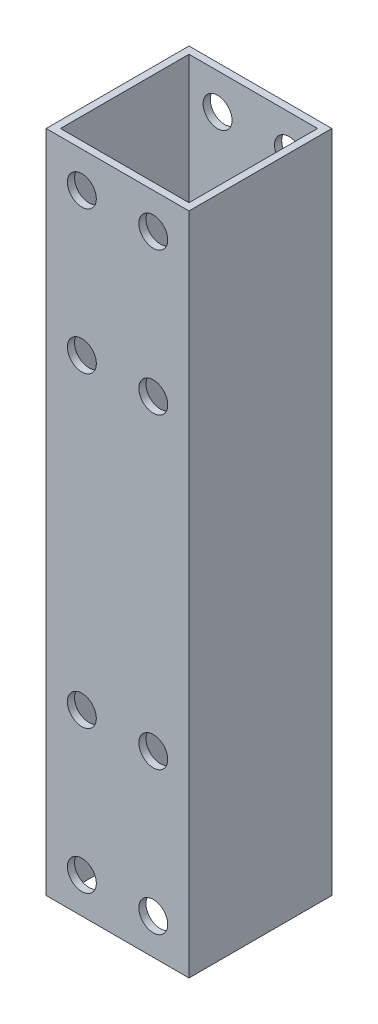
SolidWorks part; units mm, degrees
material "6061 合金"
ref_plane "前视基准面" through (0, 0, 0) normal (0, 0, 1) x (1, 0, 0)
ref_plane "上视基准面" through (0, 0, 0) normal (0, 1, 0) x (1, 0, 0)
ref_plane "右视基准面" through (0, 0, 0) normal (1, 0, 0) x (0, 0, -1)
sketch "草图1" plane through (0, 0, 0) normal (0, 1, 0) x (1, 0, 0)
  line L0 (-9, 9) -> (9, 9)
  line L1 (-10, 10) -> (10, 10)
  line L2 (-10, 10) -> (-10, -10)
  line L3 (-10, -10) -> (10, -10)
  line L4 (10, 10) -> (10, -10)
  line L5 (0, -10) -> (0, 10) construction
  line L6 (-10, 0) -> (10, 0) construction
  line L7 (9, 9) -> (9, -9)
  line L8 (-9, -9) -> (9, -9)
  line L9 (-9, 9) -> (-9, -9)
  point P0 (0, 0)
  dimension "D1" = 20
  dimension "D2" = 20
  dimension "D3" = 1
extrude "凸台-拉伸1" add sketch "草图1" along normal blind 93
sketch "草图2" plane through (0, 0, 10) normal (0, 0, 1) x (1, 0, 0)
  line L0 (-10, 0) -> (10, 0) construction
  line L1 (-5, 25) -> (5, 25) construction
  line L2 (-5, 25) -> (-5, 5) construction
  line L3 (-5, 5) -> (5, 5) construction
  line L4 (5, 25) -> (5, 5) construction
  line L5 (0, 5) -> (0, 25) construction
  line L6 (-5, 15) -> (5, 15) construction
  line L7 (-10, 93) -> (10, 93) construction
  line L8 (-5, 88) -> (5, 88) construction
  line L9 (-5, 88) -> (-5, 68) construction
  line L10 (-5, 68) -> (5, 68) construction
  line L11 (5, 88) -> (5, 68) construction
  line L12 (0, 68) -> (0, 88) construction
  line L13 (-5, 78) -> (5, 78) construction
  circle A0 centre (-5, 5) radius 2.025
  circle A1 centre (-5, 25) radius 2.025
  circle A2 centre (5, 25) radius 2.025
  circle A3 centre (5, 5) radius 2.025
  circle A4 centre (5, 88) radius 2.025
  circle A7 centre (-5, 88) radius 2.025
  circle A8 centre (-5, 68) radius 2.025
  circle A9 centre (5, 68) radius 2.025
  point P0 (0, 15)
  point P10 (0, 78)
  dimension "D5" = 20
  dimension "D9" = 4.05
  dimension "D1" = 5
  dimension "D2" = 20
  dimension "D3" = 10
  dimension "D4" = 0
  dimension "D6" = 0
  dimension "D7" = 10
  dimension "D8" = 5
  dimension "D10" = 63
extrude "切除-拉伸1" cut sketch "草图2" against normal through all
